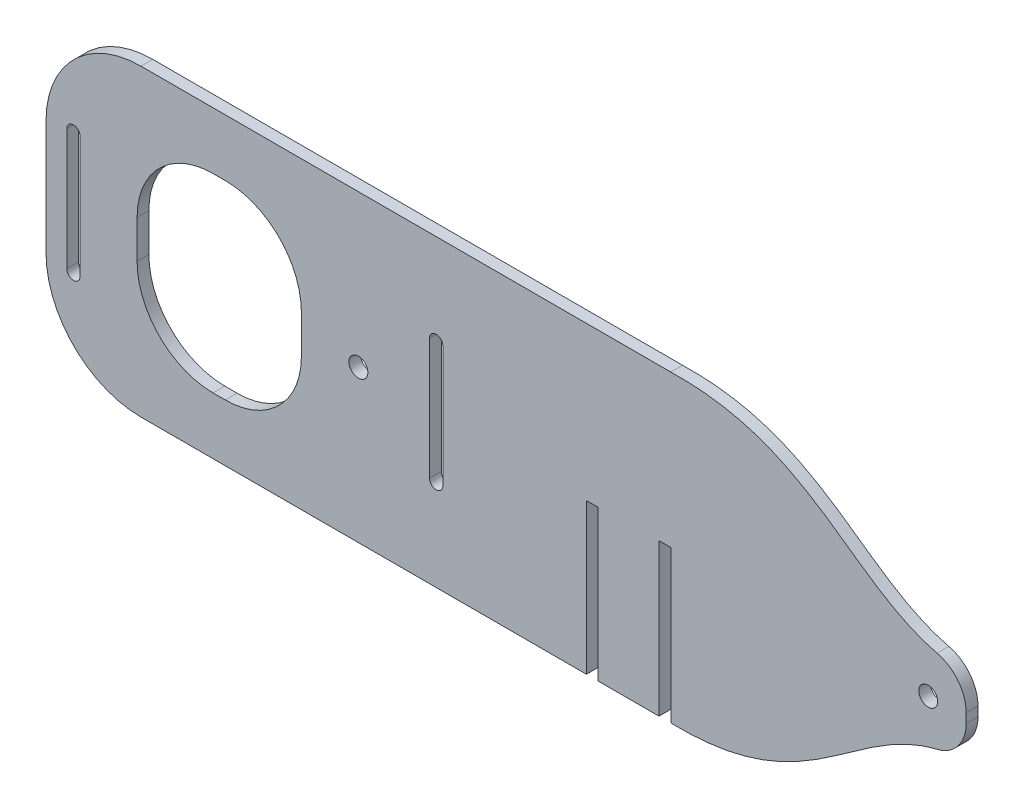
SolidWorks part; units mm, degrees
material "Teak"
ref_plane "Front Plane" through (0, 0, 0) normal (0, 0, 1) x (1, 0, 0)
ref_plane "Top Plane" through (0, 0, 0) normal (0, 1, 0) x (1, 0, 0)
ref_plane "Right Plane" through (0, 0, 0) normal (1, 0, 0) x (0, 0, -1)
sketch "Sketch1" plane through (0, 0, 0) normal (0, 0, 1) x (1, 0, 0)
  line L0 (-82.225, 0) -> (0, 0) construction
  line L1 (-82.225, -40) -> (82.225, -40)
  line L2 (-82.225, -40) -> (-82.225, 40)
  line L3 (-82.225, 40) -> (82.225, 40)
  line L4 (82.225, -40) -> (82.225, 40)
  line L5 (-82.225, -40) -> (82.225, 40) construction
  line L6 (-82.225, 40) -> (82.225, -40) construction
  line L7 (-75, 13.47) -> (-75, 0) construction
  line L8 (-76.75, -15.97) -> (-76.75, 15.97)
  line L9 (-73.25, -15.97) -> (-73.25, 15.97)
  line L10 (18.725, -15.97) -> (18.725, 15.97)
  line L11 (22.225, -15.97) -> (22.225, 15.97)
  line L13 (20.475, 13.47) -> (20.475, 0) construction
  line L14 (13.25, 0) -> (95.475, 0) construction
  line L15 (-58.25, -25) -> (-15, -25)
  line L16 (-58.25, -25) -> (-58.25, 25)
  line L17 (-58.25, 25) -> (-15, 25)
  line L18 (-15, -25) -> (-15, 25)
  line L19 (-58.25, -25) -> (-15, 25) construction
  line L20 (-58.25, 25) -> (-15, -25) construction
  circle A0 centre (0, 0) radius 2.5
  arc A1 (-76.75, 15.97) -> (-73.25, 15.97) centre (-75, 15.97) cw
  arc A2 (-76.75, -15.97) -> (-73.25, -15.97) centre (-75, -15.97) ccw
  arc A3 (18.725, 15.97) -> (22.225, 15.97) centre (20.475, 15.97) cw
  arc A4 (18.725, -15.97) -> (22.225, -15.97) centre (20.475, -15.97) ccw
  point P0 (0, 0)
  point P11 (-73.25, 0)
  point P13 (-36.625, 0)
  point P19 (-76.75, 0)
  point P25 (22.225, 0)
  point P32 (18.725, 0)
  dimension "D3" = 5
  dimension "D5" = 7.225
  dimension "D2" = 80
  dimension "D4" = 13.47
  dimension "D6" = 2.5
  dimension "D7" = 1.75
  dimension "D9" = 60
  dimension "D10" = 15
  dimension "D11" = 15
  dimension "D12" = 75
  dimension "D13" = 15
  dimension "D8" = 2
extrude "Boss-Extrude1" add sketch "Sketch1" along normal blind 3.1
sketch "Sketch2" plane through (0, 0, 3.1) normal (0, 0, 1) x (1, 0, 0)
  line L0 (60.025, -40) -> (63.125, -40)
  line L1 (60.025, -40) -> (60.025, -0.4036)
  line L2 (63.125, -40) -> (63.125, -0.4036)
  line L3 (60.025, -0.4036) -> (63.125, -0.4036)
  line L6 (-82.225, -40) -> (82.225, -40) construction
  line L10 (82.225, -40) -> (82.225, 0)
  line L11 (82.225, -40) -> (79.125, -40)
  line L12 (82.225, 0) -> (79.125, 0)
  line L13 (79.125, -40) -> (79.125, 0)
  line L14 (82.225, -40) -> (82.225, 40) construction
  dimension "D1" = 3.1
  dimension "D2" = 16
  dimension "D3" = 3.1
extrude "Cut-Extrude1" cut sketch "Sketch2" against normal through all
fillet "Fillet1" radius 25 2 edges at (-82.225, -40, 1.55) (-82.225, 40, 1.55)
sketch "Sketch3" plane through (0, 0, 3.1) normal (0, 0, 1) x (1, 0, 0)
  line L0 (82.225, 40) -> (82.225, -40)
  line L1 (82.225, 0) -> (195.5407, 0) construction
  line L3 (160, 10) -> (160, -10)
  circle A0 centre (150, 0) radius 2.5
  spline S0 degree 3 poles (82.225, -40) (100.7909, -40.4404) (122.9981, -29.67) (145.6323, -10.1637) (160, -10) knots 0 0 0 0 0.531249 1 1 1 1
  spline S1 degree 3 poles (82.225, 40) (100.7909, 40.4404) (122.9981, 29.67) (145.6323, 10.1637) (160, 10) knots 0 0 0 0 0.531249 1 1 1 1
  point P13 (160, 0)
  dimension "D2" = 5
  dimension "D1" = 10
  dimension "D3" = 150
  dimension "D4" = 0
  dimension "D5" = 10
extrude "Boss-Extrude2" add sketch "Sketch3" against normal blind 3.1 contours L0 L3
fillet "Fillet3" radius 10 2 edges at (160, -10, 1.55) (160, 10, 1.55)
fillet "Fillet4" radius 20 4 edges at (-15, 25, 1.55) (-58.25, 25, 1.55) (-15, -25, 1.55) (-58.25, -25, 1.55)
equation "\"thick\" = 3.1mm"
equation "\"small_bearing_outer\"=12.9mm"
equation "\"servo1_L\"=40.7mm"
equation "\"servo1_W\"=20.5mm"
equation "\"servo1_H\"=43.5mm"
equation "\"servo1_hL\"=49mm"
equation "\"servo1_hW\"=10mm"
equation "\"servo1_H2\"=27mm"
equation "\"large_bearing_inner\"=2.75in"
equation "\"large_bearing_outer\"=4.75in"
equation "\"large_bearing_thick\"=3/8in"
equation "\"large_bearing_h1\"=3.25in"
equation "\"large_bearing_h2\"=4.25in"
equation "\"D1@Boss-Extrude1\"=\"thick\""
equation "\"D3@Sketch2\"=\"thick\""
equation "\"D1@Sketch2\"=\"thick\""
equation "\"D5@Sketch3\"=\"D1@Sketch3\""
equation "\"D5@Sketch1\"=(4*\"thick\")-(6.35/2)-2mm"
